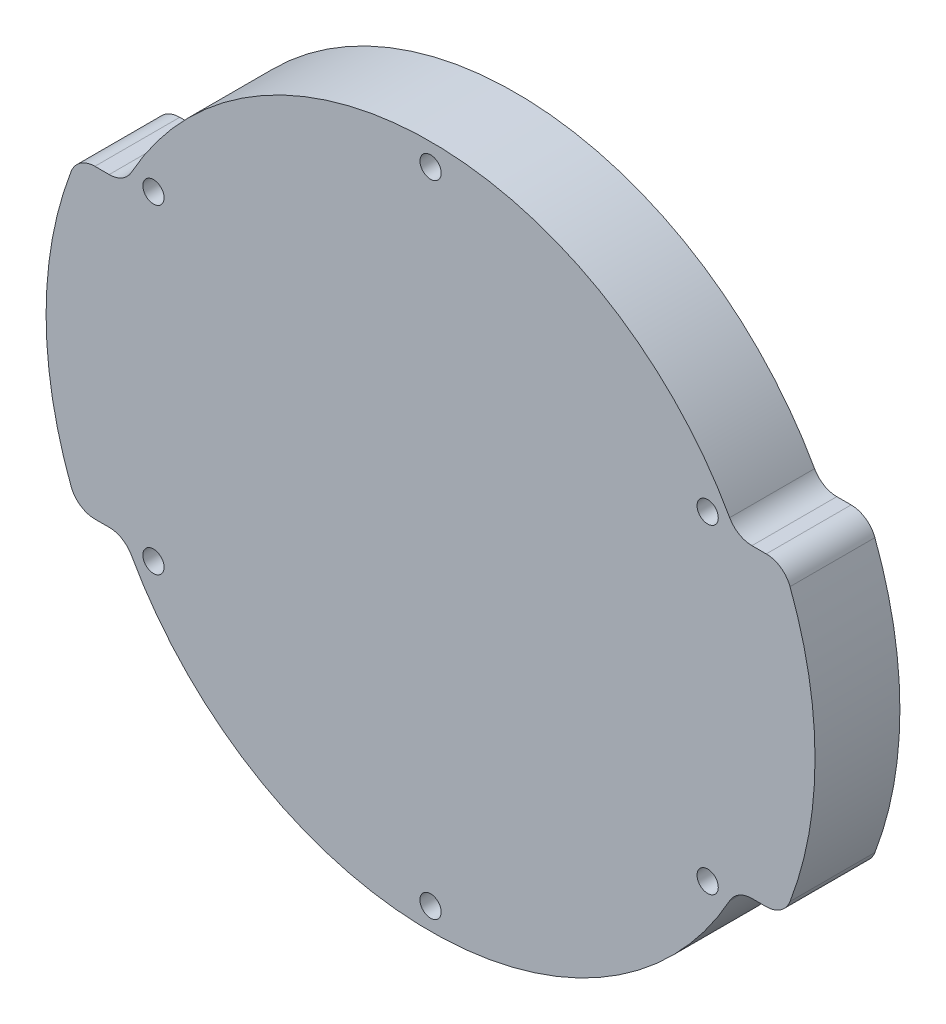
SolidWorks part; units mm, degrees
ref_plane "前视" through (0, 0, 0) normal (0, 0, 1) x (1, 0, 0)
ref_plane "上视" through (0, 0, 0) normal (0, 1, 0) x (1, 0, 0)
ref_plane "右视" through (0, 0, 0) normal (1, 0, 0) x (0, 0, -1)
sketch "草图1" plane through (0, 0, 0) normal (0, 0, 1) x (1, 0, 0)
  circle A0 centre (0, 0) radius 45.3
extrude "凸台-拉伸1" add sketch "草图1" along normal blind 10
sketch "草图2" plane through (0, 0, 10) normal (0, 0, 1) x (1, 0, 0)
  line L0 (-47.3402, 18) -> (55.6392, 18) construction
  line L1 (-63.5717, -18) -> (57.082, -18) construction
  line L2 (-36.0568, 18) -> (-41.5703, 18)
  line L3 (-36.0568, -18) -> (-41.7346, -18)
  line L4 (36.0568, -18) -> (41.7346, -18)
  line L5 (36.0568, 18) -> (41.5703, 18)
  arc A0 (36.0568, 18) -> (-36.0568, 18) centre (0, 0) ccw
  arc A1 (-36.0568, -18) -> (36.0568, -18) centre (0, 0) ccw
  circle A2 centre (0, 0) radius 45.3 construction
  arc A3 (41.5703, 18) -> (-41.5703, 18) centre (0, 0) ccw
  arc A4 (-41.7346, -18) -> (41.7346, -18) centre (0, 0) ccw
  dimension "D1" = 18
  dimension "D2" = 18
extrude "切除-拉伸1" cut sketch "草图2" against normal through all
fillet "圆角1" radius 3 8 edges at (36.0568, 18, 5) (41.5703, 18, 5) (41.5703, -18, 5) (36.0568, -18, 5) (-36.0568, -18, 5) (-41.5703, -18, 5) (-41.5703, 18, 5) (-36.0568, 18, 5)
sketch "草图3" plane through (0, 0, 10) normal (0, 0, 1) x (1, 0, 0)
  circle A0 centre (0, 37.7) radius 1.25
  circle A1 centre (32.6492, 18.85) radius 1.25
  circle A2 centre (32.6492, -18.85) radius 1.25
  circle A3 centre (0, -37.7) radius 1.25
  circle A4 centre (-32.6492, -18.85) radius 1.25
  circle A5 centre (-32.6492, 18.85) radius 1.25
  point P16 (0, 0)
  dimension "D1" = 2.5
  dimension "D2" = 37.7
  dimension "D3" = 6
extrude "切除-拉伸2" cut sketch "草图3" against normal through all
